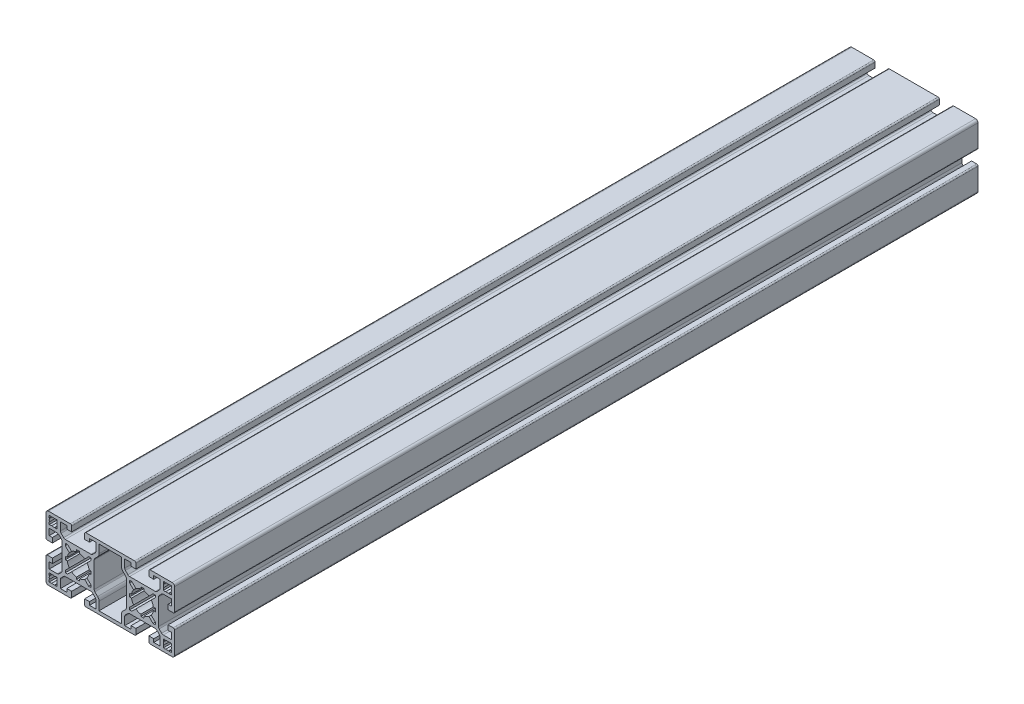
SolidWorks part; units mm, degrees
material "6063-T5"
ref_plane "Plano frontal" through (0, 0, 0) normal (0, 0, 1) x (1, 0, 0)
ref_plane "Plano superior" through (0, 0, 0) normal (0, 1, 0) x (1, 0, 0)
ref_plane "Plano direito" through (0, 0, 0) normal (1, 0, 0) x (0, 0, -1)
sketch "Esboço1" plane through (0, 0, 0) normal (0, 0, 1) x (1, 0, 0)
  line L0 (-33, 18) -> (-33, 16.5858)
  line L1 (-38.5, 20) -> (-24.85, 20)
  line L2 (-40, 18.5) -> (-40, 4.85)
  line L3 (-31, 18) -> (-27.05, 18)
  line L4 (-33, 18) -> (-34.4142, 18)
  line L5 (-30.5607, 11.9749) -> (-29.0251, 10.4393)
  line L6 (-27.9645, 10) -> (-12.0355, 10)
  line L7 (-34.4142, 18) -> (-34.5869, 17.8273)
  line L8 (-36.5858, 18) -> (-36.4131, 17.8273)
  line L9 (-33, 13) -> (-34.4142, 13)
  line L10 (-33, 13) -> (-33, 14.4142)
  line L11 (-36, 7.05) -> (-36, 4.05)
  line L12 (-33, 14.4142) -> (-33.1727, 14.5869)
  line L13 (-28, 6.5858) -> (-25.4989, 4.0847)
  line L14 (-21, 8) -> (-19, 8)
  line L15 (-21, 8) -> (-21, 6.7766)
  line L16 (-33, 16.5858) -> (-33.1727, 16.4131)
  line L17 (-28, 8) -> (-28, 6.5858)
  line L18 (-38, 13) -> (-38, 14.4142)
  line L19 (-38, 13) -> (-36.5858, 13)
  line L20 (-36.5858, 13) -> (-36.4131, 13.1727)
  line L21 (-34.4142, 13) -> (-34.5869, 13.1727)
  line L22 (-30, 7.9645) -> (-30, -7.9645)
  line L23 (-38, -11) -> (-38, -7.05)
  line L24 (-38, -14.4142) -> (-37.8273, -14.5869)
  line L25 (-7, 18) -> (-7, 12.8284)
  line L26 (-38, 18) -> (-36.5858, 18)
  line L27 (-38, 18) -> (-38, 16.5858)
  line L28 (-9.5607, 9.0251) -> (-7.8787, 10.7071)
  line L29 (-31.9749, -10.5607) -> (-30.4393, -9.0251)
  line L30 (-28, -1) -> (-26.7766, -1)
  line L31 (-9, -18) -> (-12.95, -18)
  line L32 (-24.05, 19.2) -> (-24.05, 16)
  line L33 (-9.4393, -11.9749) -> (-10.9749, -10.4393)
  line L34 (-38, 7.05) -> (-36, 7.05)
  line L35 (-19, -8) -> (-19, -6.7766)
  line L36 (-15.95, -19.2) -> (-15.95, -16)
  line L37 (-12.95, 16) -> (-15.95, 16)
  line L38 (-38, 11) -> (-33.0355, 11)
  line L39 (-31, 18) -> (-31, 13.0355)
  line L40 (-12, -6.5858) -> (-14.5011, -4.0847)
  line L41 (-13.4142, 8) -> (-15.9153, 5.4989)
  line L42 (-12, -8) -> (-12, -6.5858)
  line L43 (-12, 1) -> (-13.2234, 1)
  line L44 (-27.05, 18) -> (-27.05, 16)
  line L45 (-9, -18) -> (-9, -13.0355)
  line L46 (-28, 8) -> (-26.5858, 8)
  line L47 (-26.5858, 8) -> (-24.0847, 5.4989)
  line L48 (-27.05, 16) -> (-24.05, 16)
  line L49 (-12.95, -18) -> (-12.95, -16)
  line L50 (-38, -16.5858) -> (-37.8273, -16.4131)
  line L51 (-12, 8) -> (-13.4142, 8)
  line L52 (-39.2, -4.05) -> (-36, -4.05)
  line L53 (-12, -8) -> (-13.4142, -8)
  line L54 (-27.05, -16) -> (-24.05, -16)
  line L55 (-26.5858, -8) -> (-24.0847, -5.4989)
  line L56 (-28, -8) -> (-26.5858, -8)
  line L57 (-39.2, 4.05) -> (-36, 4.05)
  line L58 (-27.05, -18) -> (-27.05, -16)
  line L59 (-38, 16.5858) -> (-37.8273, 16.4131)
  line L60 (-12, -1) -> (-13.2234, -1)
  line L61 (-12.95, 18) -> (-12.95, 16)
  line L62 (-9, 18) -> (-9, 13.0355)
  line L63 (-13.4142, -8) -> (-15.9153, -5.4989)
  line L64 (-31, -18) -> (-31, -13.0355)
  line L65 (-12, 8) -> (-12, 6.5858)
  line L66 (-12, 6.5858) -> (-14.5011, 4.0847)
  line L67 (-38, -11) -> (-33.0355, -11)
  line L68 (-12.95, -16) -> (-15.95, -16)
  line L69 (-38, -7.05) -> (-36, -7.05)
  line L70 (-15.95, 19.2) -> (-15.95, 16)
  line L71 (-24.05, -19.2) -> (-24.05, -16)
  line L72 (-9.5607, -9.0251) -> (-7.8787, -10.7071)
  line L73 (-19, 8) -> (-19, 6.7766)
  line L74 (-38, -18) -> (-38, -16.5858)
  line L75 (-9.4393, 11.9749) -> (-10.9749, 10.4393)
  line L76 (-38, -18) -> (-36.5858, -18)
  line L77 (-9, 18) -> (-12.95, 18)
  line L78 (-7, -18) -> (-7, -12.8284)
  line L79 (-34.4142, -13) -> (-34.5869, -13.1727)
  line L80 (-36.5858, -13) -> (-36.4131, -13.1727)
  line L81 (-38, -13) -> (-36.5858, -13)
  line L82 (-38, -13) -> (-38, -14.4142)
  line L83 (-28, -8) -> (-28, -6.5858)
  line L84 (-33, -16.5858) -> (-33.1727, -16.4131)
  line L85 (-21, -8) -> (-21, -6.7766)
  line L86 (-21, -8) -> (-19, -8)
  line L87 (-28, -6.5858) -> (-25.4989, -4.0847)
  line L88 (-33, -14.4142) -> (-33.1727, -14.5869)
  line L89 (-36, -7.05) -> (-36, -4.05)
  line L90 (-33, -13) -> (-33, -14.4142)
  line L91 (-33, -13) -> (-34.4142, -13)
  line L92 (-36.5858, -18) -> (-36.4131, -17.8273)
  line L93 (-34.4142, -18) -> (-34.5869, -17.8273)
  line L94 (-27.9645, -10) -> (-12.0355, -10)
  line L95 (-30.5607, -11.9749) -> (-29.0251, -10.4393)
  line L96 (-33, -18) -> (-34.4142, -18)
  line L97 (-31, -18) -> (-27.05, -18)
  line L98 (-40, -18.5) -> (-40, -4.85)
  line L99 (-38.5, -20) -> (-24.85, -20)
  line L100 (-33, -18) -> (-33, -16.5858)
  line L101 (-28, 1) -> (-28, -1)
  line L102 (-12, -1) -> (-12, 1)
  line L103 (-10, 7.9645) -> (-10, -7.9645)
  line L104 (-15.15, 20) -> (15.15, 20)
  line L105 (-15.15, -20) -> (15.15, -20)
  line L108 (0, 25.8211) -> (0, -27.4656) construction
  line L109 (38, 11) -> (38, 7.05)
  line L110 (38, 14.4142) -> (37.8273, 14.5869)
  line L111 (-28, 1) -> (-26.7766, 1)
  line L112 (31.9749, 10.5607) -> (30.4393, 9.0251)
  line L113 (28, 1) -> (26.7766, 1)
  line L118 (10, 7.9645) -> (10, -7.9645)
  line L119 (12, -1) -> (12, 1)
  line L120 (-31.9749, 10.5607) -> (-30.4393, 9.0251)
  line L121 (28, 1) -> (28, -1)
  line L122 (33, -18) -> (33, -16.5858)
  line L123 (-38, 14.4142) -> (-37.8273, 14.5869)
  line L124 (38.5, -20) -> (24.85, -20)
  line L125 (40, -18.5) -> (40, -4.85)
  line L126 (31, -18) -> (27.05, -18)
  line L127 (33, -18) -> (34.4142, -18)
  line L128 (-38, 11) -> (-38, 7.05)
  line L129 (30.5607, -11.9749) -> (29.0251, -10.4393)
  line L130 (27.9645, -10) -> (12.0355, -10)
  line L131 (34.4142, -18) -> (34.5869, -17.8273)
  line L132 (36.5858, -18) -> (36.4131, -17.8273)
  line L133 (33, -13) -> (34.4142, -13)
  line L134 (33, -13) -> (33, -14.4142)
  line L135 (36, -7.05) -> (36, -4.05)
  line L136 (33, -14.4142) -> (33.1727, -14.5869)
  line L137 (28, -6.5858) -> (25.4989, -4.0847)
  line L138 (21, -8) -> (19, -8)
  line L139 (21, -8) -> (21, -6.7766)
  line L140 (33, -16.5858) -> (33.1727, -16.4131)
  line L141 (28, -8) -> (28, -6.5858)
  line L142 (38, -13) -> (38, -14.4142)
  line L143 (38, -13) -> (36.5858, -13)
  line L144 (36.5858, -13) -> (36.4131, -13.1727)
  line L145 (34.4142, -13) -> (34.5869, -13.1727)
  line L146 (7, -18) -> (7, -12.8284)
  line L147 (9, 18) -> (12.95, 18)
  line L148 (38, -18) -> (36.5858, -18)
  line L149 (9.4393, 11.9749) -> (10.9749, 10.4393)
  line L150 (38, -18) -> (38, -16.5858)
  line L151 (19, 8) -> (19, 6.7766)
  line L152 (9.5607, -9.0251) -> (7.8787, -10.7071)
  line L153 (24.05, -19.2) -> (24.05, -16)
  line L154 (15.95, 19.2) -> (15.95, 16)
  line L155 (38, -7.05) -> (36, -7.05)
  line L156 (12.95, -16) -> (15.95, -16)
  line L157 (38, -11) -> (33.0355, -11)
  line L158 (12, 6.5858) -> (14.5011, 4.0847)
  line L159 (12, 8) -> (12, 6.5858)
  line L160 (31, -18) -> (31, -13.0355)
  line L161 (13.4142, -8) -> (15.9153, -5.4989)
  line L162 (9, 18) -> (9, 13.0355)
  line L163 (12.95, 18) -> (12.95, 16)
  line L164 (12, -1) -> (13.2234, -1)
  line L165 (38, 16.5858) -> (37.8273, 16.4131)
  line L166 (27.05, -18) -> (27.05, -16)
  line L167 (39.2, 4.05) -> (36, 4.05)
  line L168 (28, -8) -> (26.5858, -8)
  line L169 (26.5858, -8) -> (24.0847, -5.4989)
  line L170 (27.05, -16) -> (24.05, -16)
  line L171 (12, -8) -> (13.4142, -8)
  line L172 (39.2, -4.05) -> (36, -4.05)
  line L173 (-1.5, 20) -> (-15.15, 20) [skipped]
  line L174 (0, 18.5) -> (0, 4.85) [skipped]
  line L175 (12, 8) -> (13.4142, 8)
  line L176 (0, -18.5) -> (0, -4.85) [skipped]
  line L177 (-0.8, 4.05) -> (-4, 4.05) [skipped]
  line L178 (-0.8, -4.05) -> (-4, -4.05) [skipped]
  line L179 (-1.5, -20) -> (-15.15, -20) [skipped]
  line L180 (38, -16.5858) -> (37.8273, -16.4131)
  line L181 (-2, 11) -> (-6.9645, 11) [skipped]
  line L182 (-7, 13) -> (-5.5858, 13) [skipped]
  line L183 (-7, 18) -> (-5.5858, 18) [skipped]
  line L184 (-2, 18) -> (-3.4142, 18) [skipped]
  line L185 (-2, 18) -> (-2, 16.5858) [skipped]
  line L186 (-2, 13) -> (-2, 14.4142) [skipped]
  line L187 (-2, 13) -> (-3.4142, 13) [skipped]
  line L188 (-2, 11) -> (-2, 7.05) [skipped]
  line L189 (-2, 7.05) -> (-4, 7.05) [skipped]
  line L190 (-4, 7.05) -> (-4, 4.05) [skipped]
  line L191 (-7, 13) -> (-7, 14.4142) [skipped]
  line L192 (-5.5858, 13) -> (-5.4131, 13.1727) [skipped]
  line L193 (-2, 14.4142) -> (-2.1727, 14.5869) [skipped]
  line L194 (-2, 16.5858) -> (-2.1727, 16.4131) [skipped]
  line L195 (-3.4142, 13) -> (-3.5869, 13.1727) [skipped]
  line L196 (-7, 14.4142) -> (-6.8273, 14.5869) [skipped]
  line L197 (-3.4142, 18) -> (-3.5869, 17.8273) [skipped]
  line L198 (-5.5858, 18) -> (-5.4131, 17.8273) [skipped]
  line L199 (-7, 18) -> (-7, 16.5858) [skipped]
  line L200 (-7, 16.5858) -> (-6.8273, 16.4131) [skipped]
  line L201 (-8.0251, 10.5607) -> (-9.5607, 9.0251) [skipped]
  line L202 (-8.0251, -10.5607) -> (-9.5607, -9.0251) [skipped]
  line L203 (-2, -11) -> (-6.9645, -11) [skipped]
  line L204 (-2, -11) -> (-2, -7.05) [skipped]
  line L205 (-2, -7.05) -> (-4, -7.05) [skipped]
  line L206 (-4, -7.05) -> (-4, -4.05) [skipped]
  line L207 (-7, -18) -> (-7, -16.5858) [skipped]
  line L208 (-7, -18) -> (-5.5858, -18) [skipped]
  line L209 (-5.5858, -18) -> (-5.4131, -17.8273) [skipped]
  line L210 (-3.4142, -18) -> (-3.5869, -17.8273) [skipped]
  line L211 (-7, -13) -> (-5.5858, -13) [skipped]
  line L212 (-7, -13) -> (-7, -14.4142) [skipped]
  line L213 (-7, -14.4142) -> (-6.8273, -14.5869) [skipped]
  line L214 (-7, -16.5858) -> (-6.8273, -16.4131) [skipped]
  line L215 (-2, -13) -> (-2, -14.4142) [skipped]
  line L216 (-2, -13) -> (-3.4142, -13) [skipped]
  line L217 (-3.4142, -13) -> (-3.5869, -13.1727) [skipped]
  line L218 (-5.5858, -13) -> (-5.4131, -13.1727) [skipped]
  line L219 (-2, -18) -> (-3.4142, -18) [skipped]
  line L220 (-2, -18) -> (-2, -16.5858) [skipped]
  line L221 (-2, -16.5858) -> (-2.1727, -16.4131) [skipped]
  line L222 (-2, -14.4142) -> (-2.1727, -14.5869) [skipped]
  line L223 (12.95, -18) -> (12.95, -16)
  line L224 (-40, -18.5) -> (-40, -4.85) [skipped]
  line L225 (27.05, 16) -> (24.05, 16)
  line L226 (26.5858, 8) -> (24.0847, 5.4989)
  line L227 (28, 8) -> (26.5858, 8)
  line L228 (9, -18) -> (9, -13.0355)
  line L229 (27.05, 18) -> (27.05, 16)
  line L230 (12, 1) -> (13.2234, 1)
  line L231 (12, -8) -> (12, -6.5858)
  line L232 (13.4142, 8) -> (15.9153, 5.4989)
  line L233 (12, -6.5858) -> (14.5011, -4.0847)
  line L234 (31, 18) -> (31, 13.0355)
  line L235 (38, 11) -> (33.0355, 11)
  line L236 (12.95, 16) -> (15.95, 16)
  line L237 (15.95, -19.2) -> (15.95, -16)
  line L238 (19, -8) -> (19, -6.7766)
  line L239 (38, 7.05) -> (36, 7.05)
  line L240 (9.4393, -11.9749) -> (10.9749, -10.4393)
  line L241 (24.05, 19.2) -> (24.05, 16)
  line L242 (9, -18) -> (12.95, -18)
  line L243 (28, -1) -> (26.7766, -1)
  line L244 (31.9749, -10.5607) -> (30.4393, -9.0251)
  line L245 (9.5607, 9.0251) -> (7.8787, 10.7071)
  line L246 (38, 18) -> (38, 16.5858)
  line L247 (38, 18) -> (36.5858, 18)
  line L248 (7, 18) -> (7, 12.8284)
  line L249 (38, -14.4142) -> (37.8273, -14.5869)
  line L250 (38, -11) -> (38, -7.05)
  line L251 (30, 7.9645) -> (30, -7.9645)
  line L252 (34.4142, 13) -> (34.5869, 13.1727)
  line L253 (36.5858, 13) -> (36.4131, 13.1727)
  line L254 (38, 13) -> (36.5858, 13)
  line L255 (38, 13) -> (38, 14.4142)
  line L256 (28, 8) -> (28, 6.5858)
  line L257 (33, 16.5858) -> (33.1727, 16.4131)
  line L258 (21, 8) -> (21, 6.7766)
  line L259 (21, 8) -> (19, 8)
  line L260 (28, 6.5858) -> (25.4989, 4.0847)
  line L261 (33, 14.4142) -> (33.1727, 14.5869)
  line L262 (36, 7.05) -> (36, 4.05)
  line L263 (33, 13) -> (33, 14.4142)
  line L264 (33, 13) -> (34.4142, 13)
  line L265 (36.5858, 18) -> (36.4131, 17.8273)
  line L266 (34.4142, 18) -> (34.5869, 17.8273)
  line L267 (27.9645, 10) -> (12.0355, 10)
  line L268 (30.5607, 11.9749) -> (29.0251, 10.4393)
  line L269 (33, 18) -> (34.4142, 18)
  line L270 (31, 18) -> (27.05, 18)
  line L271 (40, 18.5) -> (40, 4.85)
  line L272 (38.5, 20) -> (24.85, 20)
  line L273 (33, 18) -> (33, 16.5858)
  line L274 (-7, 18) -> (7, 18)
  line L275 (-7, -18) -> (7, -18)
  line L316 (-9, -18) -> (-12.95, -18) [skipped]
  line L317 (-9.4393, -11.9749) -> (-10.9749, -10.4393) [skipped]
  line L318 (-12, -6.5858) -> (-14.5011, -4.0847) [skipped]
  line L320 (-19, -8) -> (-19, -6.7766) [skipped]
  line L321 (-12, -8) -> (-12, -6.5858) [skipped]
  line L322 (-15.95, -19.2) -> (-15.95, -16) [skipped]
  line L323 (-9, -18) -> (-9, -13.0355) [skipped]
  line L324 (-12.95, -18) -> (-12.95, -16) [skipped]
  line L325 (-12, -8) -> (-13.4142, -8) [skipped]
  line L326 (-13.4142, -8) -> (-15.9153, -5.4989) [skipped]
  line L327 (-12.95, -16) -> (-15.95, -16) [skipped]
  line L329 (-12, -1) -> (-13.2234, -1) [skipped]
  line L330 (-38, -13) -> (-36.5858, -13) [skipped]
  line L331 (-38.5, -20) -> (-24.85, -20) [skipped]
  line L332 (-38, -11) -> (-38, -7.05) [skipped]
  line L333 (-38, -13) -> (-38, -14.4142) [skipped]
  line L334 (-31.9749, -10.5607) -> (-30.4393, -9.0251) [skipped]
  line L335 (-38, -14.4142) -> (-37.8273, -14.5869) [skipped]
  line L336 (-38, -16.5858) -> (-37.8273, -16.4131) [skipped]
  line L337 (-33, -13) -> (-33, -14.4142) [skipped]
  line L338 (-33, -13) -> (-34.4142, -13) [skipped]
  line L339 (-27.05, -16) -> (-24.05, -16) [skipped]
  line L340 (-34.4142, -13) -> (-34.5869, -13.1727) [skipped]
  line L341 (-26.5858, -8) -> (-24.0847, -5.4989) [skipped]
  line L342 (-28, -1) -> (-26.7766, -1) [skipped]
  line L343 (-36.5858, -13) -> (-36.4131, -13.1727) [skipped]
  line L344 (-28, -8) -> (-26.5858, -8) [skipped]
  line L345 (-33, -18) -> (-34.4142, -18) [skipped]
  line L346 (-33, -18) -> (-33, -16.5858) [skipped]
  line L347 (-33, -16.5858) -> (-33.1727, -16.4131) [skipped]
  line L348 (-33, -14.4142) -> (-33.1727, -14.5869) [skipped]
  line L349 (-38, -18) -> (-38, -16.5858) [skipped]
  line L350 (-38, -18) -> (-36.5858, -18) [skipped]
  line L351 (-39.2, -4.05) -> (-36, -4.05) [skipped]
  line L352 (-27.05, -18) -> (-27.05, -16) [skipped]
  line L353 (-31, -18) -> (-31, -13.0355) [skipped]
  line L354 (-38, -11) -> (-33.0355, -11) [skipped]
  line L355 (-38, -7.05) -> (-36, -7.05) [skipped]
  line L356 (-28, -8) -> (-28, -6.5858) [skipped]
  line L357 (-28, -6.5858) -> (-25.4989, -4.0847) [skipped]
  line L358 (-36, -7.05) -> (-36, -4.05) [skipped]
  line L359 (-24.05, -19.2) -> (-24.05, -16) [skipped]
  line L360 (-36.5858, -18) -> (-36.4131, -17.8273) [skipped]
  line L361 (-21, -8) -> (-21, -6.7766) [skipped]
  line L362 (-30.5607, -11.9749) -> (-29.0251, -10.4393) [skipped]
  line L363 (-34.4142, -18) -> (-34.5869, -17.8273) [skipped]
  line L364 (-31, -18) -> (-27.05, -18) [skipped]
  arc A0 (-30.5607, 11.9749) -> (-31, 13.0355) centre (-29.5, 13.0355) cw
  arc A1 (-37.8273, 16.4131) -> (-37.8273, 14.5869) centre (-35.5, 15.5) ccw
  arc A2 (-38.5, 20) -> (-40, 18.5) centre (-38.5, 18.5) ccw
  arc A3 (-25.4989, 4.0847) -> (-26.7766, 1) centre (-20, 0) ccw
  arc A4 (-31.9749, 10.5607) -> (-33.0355, 11) centre (-33.0355, 9.5) ccw
  arc A5 (-30, 7.9645) -> (-30.4393, 9.0251) centre (-31.5, 7.9645) ccw
  arc A6 (-40, 4.85) -> (-39.2, 4.05) centre (-39.2, 4.85) ccw
  arc A7 (-24.0847, 5.4989) -> (-21, 6.7766) centre (-20, 0) cw
  arc A8 (-34.5869, 17.8273) -> (-36.4131, 17.8273) centre (-35.5, 15.5) ccw
  arc A9 (-33.1727, 14.5869) -> (-33.1727, 16.4131) centre (-35.5, 15.5) ccw
  arc A10 (-36.4131, 13.1727) -> (-34.5869, 13.1727) centre (-35.5, 15.5) ccw
  arc A11 (-7, 12.8284) -> (-7.8787, 10.7071) centre (-10, 12.8284) cw
  arc A12 (-10, -7.9645) -> (-9.5607, -9.0251) centre (-8.5, -7.9645) ccw
  arc A13 (-14.5011, -4.0847) -> (-13.2234, -1) centre (-20, 0) ccw
  arc A14 (-15.9153, 5.4989) -> (-19, 6.7766) centre (-20, 0) ccw
  arc A15 (-9.4393, 11.9749) -> (-9, 13.0355) centre (-10.5, 13.0355) ccw
  arc A16 (-12.0355, 10) -> (-10.9749, 10.4393) centre (-12.0355, 11.5) ccw
  arc A17 (-24.85, 20) -> (-24.05, 19.2) centre (-24.85, 19.2) cw
  arc A18 (-27.9645, 10) -> (-29.0251, 10.4393) centre (-27.9645, 11.5) cw
  arc A19 (-15.15, -20) -> (-15.95, -19.2) centre (-15.15, -19.2) cw
  arc A20 (-27.9645, -10) -> (-29.0251, -10.4393) centre (-27.9645, -11.5) ccw
  arc A21 (-15.15, 20) -> (-15.95, 19.2) centre (-15.15, 19.2) ccw
  arc A22 (-14.5011, 4.0847) -> (-13.2234, 1) centre (-20, 0) cw
  arc A23 (-24.85, -20) -> (-24.05, -19.2) centre (-24.85, -19.2) ccw
  arc A24 (-12.0355, -10) -> (-10.9749, -10.4393) centre (-12.0355, -11.5) cw
  arc A25 (-9.4393, -11.9749) -> (-9, -13.0355) centre (-10.5, -13.0355) cw
  arc A26 (-15.9153, -5.4989) -> (-19, -6.7766) centre (-20, 0) cw
  arc A27 (-10, 7.9645) -> (-9.5607, 9.0251) centre (-8.5, 7.9645) cw
  arc A28 (-7, -12.8284) -> (-7.8787, -10.7071) centre (-10, -12.8284) ccw
  arc A29 (-36.4131, -13.1727) -> (-34.5869, -13.1727) centre (-35.5, -15.5) cw
  arc A30 (-33.1727, -14.5869) -> (-33.1727, -16.4131) centre (-35.5, -15.5) cw
  arc A31 (-34.5869, -17.8273) -> (-36.4131, -17.8273) centre (-35.5, -15.5) cw
  arc A32 (-24.0847, -5.4989) -> (-21, -6.7766) centre (-20, 0) ccw
  arc A33 (-40, -4.85) -> (-39.2, -4.05) centre (-39.2, -4.85) cw
  arc A34 (-30, -7.9645) -> (-30.4393, -9.0251) centre (-31.5, -7.9645) cw
  arc A35 (-31.9749, -10.5607) -> (-33.0355, -11) centre (-33.0355, -9.5) cw
  arc A36 (-25.4989, -4.0847) -> (-26.7766, -1) centre (-20, 0) cw
  arc A37 (-38.5, -20) -> (-40, -18.5) centre (-38.5, -18.5) cw
  arc A38 (-37.8273, -16.4131) -> (-37.8273, -14.5869) centre (-35.5, -15.5) cw
  arc A39 (-30.5607, -11.9749) -> (-31, -13.0355) centre (-29.5, -13.0355) ccw
  arc A40 (30.5607, -11.9749) -> (31, -13.0355) centre (29.5, -13.0355) cw
  arc A41 (37.8273, -16.4131) -> (37.8273, -14.5869) centre (35.5, -15.5) ccw
  arc A42 (38.5, -20) -> (40, -18.5) centre (38.5, -18.5) ccw
  arc A43 (25.4989, -4.0847) -> (26.7766, -1) centre (20, 0) ccw
  arc A44 (31.9749, -10.5607) -> (33.0355, -11) centre (33.0355, -9.5) ccw
  arc A45 (30, -7.9645) -> (30.4393, -9.0251) centre (31.5, -7.9645) ccw
  arc A46 (40, -4.85) -> (39.2, -4.05) centre (39.2, -4.85) ccw
  arc A47 (24.0847, -5.4989) -> (21, -6.7766) centre (20, 0) cw
  arc A48 (34.5869, -17.8273) -> (36.4131, -17.8273) centre (35.5, -15.5) ccw
  arc A49 (33.1727, -14.5869) -> (33.1727, -16.4131) centre (35.5, -15.5) ccw
  arc A50 (36.4131, -13.1727) -> (34.5869, -13.1727) centre (35.5, -15.5) ccw
  arc A51 (7, -12.8284) -> (7.8787, -10.7071) centre (10, -12.8284) cw
  arc A52 (10, 7.9645) -> (9.5607, 9.0251) centre (8.5, 7.9645) ccw
  arc A53 (15.9153, -5.4989) -> (19, -6.7766) centre (20, 0) ccw
  arc A54 (0, 18.5) -> (-1.5, 20) centre (-1.5, 18.5) ccw [skipped]
  arc A55 (-1.5, -20) -> (0, -18.5) centre (-1.5, -18.5) ccw [skipped]
  arc A56 (0, -4.85) -> (-0.8, -4.05) centre (-0.8, -4.85) ccw [skipped]
  arc A57 (0, 4.85) -> (-0.8, 4.05) centre (-0.8, 4.85) cw [skipped]
  arc A58 (-3.5869, 17.8273) -> (-5.4131, 17.8273) centre (-4.5, 15.5) ccw [skipped]
  arc A59 (-2.1727, 14.5869) -> (-2.1727, 16.4131) centre (-4.5, 15.5) ccw [skipped]
  arc A60 (-5.4131, 13.1727) -> (-3.5869, 13.1727) centre (-4.5, 15.5) ccw [skipped]
  arc A61 (-8.0251, 10.5607) -> (-6.9645, 11) centre (-6.9645, 9.5) cw [skipped]
  arc A62 (-6.8273, 16.4131) -> (-6.8273, 14.5869) centre (-4.5, 15.5) ccw [skipped]
  arc A63 (-8.0251, -10.5607) -> (-6.9645, -11) centre (-6.9645, -9.5) ccw [skipped]
  arc A64 (-2.1727, -16.4131) -> (-2.1727, -14.5869) centre (-4.5, -15.5) ccw [skipped]
  arc A65 (-5.4131, -17.8273) -> (-3.5869, -17.8273) centre (-4.5, -15.5) ccw [skipped]
  arc A66 (-6.8273, -14.5869) -> (-6.8273, -16.4131) centre (-4.5, -15.5) ccw [skipped]
  arc A67 (-3.5869, -13.1727) -> (-5.4131, -13.1727) centre (-4.5, -15.5) ccw [skipped]
  arc A68 (9.4393, -11.9749) -> (9, -13.0355) centre (10.5, -13.0355) ccw
  arc A69 (12.0355, -10) -> (10.9749, -10.4393) centre (12.0355, -11.5) ccw
  arc A70 (24.85, -20) -> (24.05, -19.2) centre (24.85, -19.2) cw
  arc A71 (14.5011, 4.0847) -> (13.2234, 1) centre (20, 0) ccw
  arc A72 (15.15, 20) -> (15.95, 19.2) centre (15.15, 19.2) cw
  arc A73 (27.9645, -10) -> (29.0251, -10.4393) centre (27.9645, -11.5) cw
  arc A74 (15.15, -20) -> (15.95, -19.2) centre (15.15, -19.2) ccw
  arc A75 (27.9645, 10) -> (29.0251, 10.4393) centre (27.9645, 11.5) ccw
  arc A76 (24.85, 20) -> (24.05, 19.2) centre (24.85, 19.2) ccw
  arc A77 (12.0355, 10) -> (10.9749, 10.4393) centre (12.0355, 11.5) cw
  arc A78 (9.4393, 11.9749) -> (9, 13.0355) centre (10.5, 13.0355) cw
  arc A79 (15.9153, 5.4989) -> (19, 6.7766) centre (20, 0) cw
  arc A80 (14.5011, -4.0847) -> (13.2234, -1) centre (20, 0) cw
  arc A81 (10, -7.9645) -> (9.5607, -9.0251) centre (8.5, -7.9645) cw
  arc A82 (7, 12.8284) -> (7.8787, 10.7071) centre (10, 12.8284) ccw
  arc A83 (36.4131, 13.1727) -> (34.5869, 13.1727) centre (35.5, 15.5) cw
  arc A84 (33.1727, 14.5869) -> (33.1727, 16.4131) centre (35.5, 15.5) cw
  arc A85 (34.5869, 17.8273) -> (36.4131, 17.8273) centre (35.5, 15.5) cw
  arc A86 (24.0847, 5.4989) -> (21, 6.7766) centre (20, 0) ccw
  arc A87 (40, 4.85) -> (39.2, 4.05) centre (39.2, 4.85) cw
  arc A88 (30, 7.9645) -> (30.4393, 9.0251) centre (31.5, 7.9645) cw
  arc A89 (31.9749, 10.5607) -> (33.0355, 11) centre (33.0355, 9.5) cw
  arc A90 (25.4989, 4.0847) -> (26.7766, 1) centre (20, 0) cw
  arc A91 (38.5, 20) -> (40, 18.5) centre (38.5, 18.5) cw
  arc A92 (37.8273, 16.4131) -> (37.8273, 14.5869) centre (35.5, 15.5) cw
  arc A93 (30.5607, 11.9749) -> (31, 13.0355) centre (29.5, 13.0355) ccw
  arc A96 (-9.4393, -11.9749) -> (-9, -13.0355) centre (-10.5, -13.0355) cw [skipped]
  arc A97 (-14.5011, -4.0847) -> (-13.2234, -1) centre (-20, 0) ccw [skipped]
  arc A98 (-10, -7.9645) -> (-9.5607, -9.0251) centre (-8.5, -7.9645) ccw [skipped]
  arc A99 (-15.9153, -5.4989) -> (-19, -6.7766) centre (-20, 0) cw [skipped]
  arc A100 (-15.15, -20) -> (-15.95, -19.2) centre (-15.15, -19.2) cw [skipped]
  arc A101 (-12.0355, -10) -> (-10.9749, -10.4393) centre (-12.0355, -11.5) cw [skipped]
  arc A102 (-31.9749, -10.5607) -> (-33.0355, -11) centre (-33.0355, -9.5) cw [skipped]
  arc A103 (-36.4131, -17.8273) -> (-34.5869, -17.8273) centre (-35.5, -15.5) ccw [skipped]
  arc A104 (-40, -18.5) -> (-38.5, -20) centre (-38.5, -18.5) ccw [skipped]
  arc A105 (-24.0847, -5.4989) -> (-21, -6.7766) centre (-20, 0) ccw [skipped]
  arc A106 (-30.5607, -11.9749) -> (-31, -13.0355) centre (-29.5, -13.0355) ccw [skipped]
  arc A107 (-27.9645, -10) -> (-29.0251, -10.4393) centre (-27.9645, -11.5) ccw [skipped]
  arc A108 (-24.85, -20) -> (-24.05, -19.2) centre (-24.85, -19.2) ccw [skipped]
  arc A109 (-25.4989, -4.0847) -> (-26.7766, -1) centre (-20, 0) cw [skipped]
  arc A110 (-37.8273, -14.5869) -> (-37.8273, -16.4131) centre (-35.5, -15.5) ccw [skipped]
  arc A111 (-34.5869, -13.1727) -> (-36.4131, -13.1727) centre (-35.5, -15.5) ccw [skipped]
  arc A112 (-33.1727, -16.4131) -> (-33.1727, -14.5869) centre (-35.5, -15.5) ccw [skipped]
  arc A113 (-40, -4.85) -> (-39.2, -4.05) centre (-39.2, -4.85) cw [skipped]
  arc A114 (-30, -7.9645) -> (-30.4393, -9.0251) centre (-31.5, -7.9645) cw [skipped]
  point P5 (-4.5, 15.5)
  point P7 (-35.5, -15.5)
  point P20 (-20, 0)
  point P31 (-4.5, 15.5)
  point P38 (-20, 0)
  point P45 (-35.5, 15.5)
  point P57 (-4.5, -15.5)
  point P66 (-4.5, -15.5)
  point P77 (-35.5, -15.5)
  point P79 (-20, 0)
  point P80 (-20, 0)
  point P81 (-20, 0)
  point P207 (-35.5, 15.5)
  dimension "D2" = 4
  dimension "D1" = 4
extrude "Ressalto-extrusão1" add sketch "Esboço1" along normal mid plane 500
